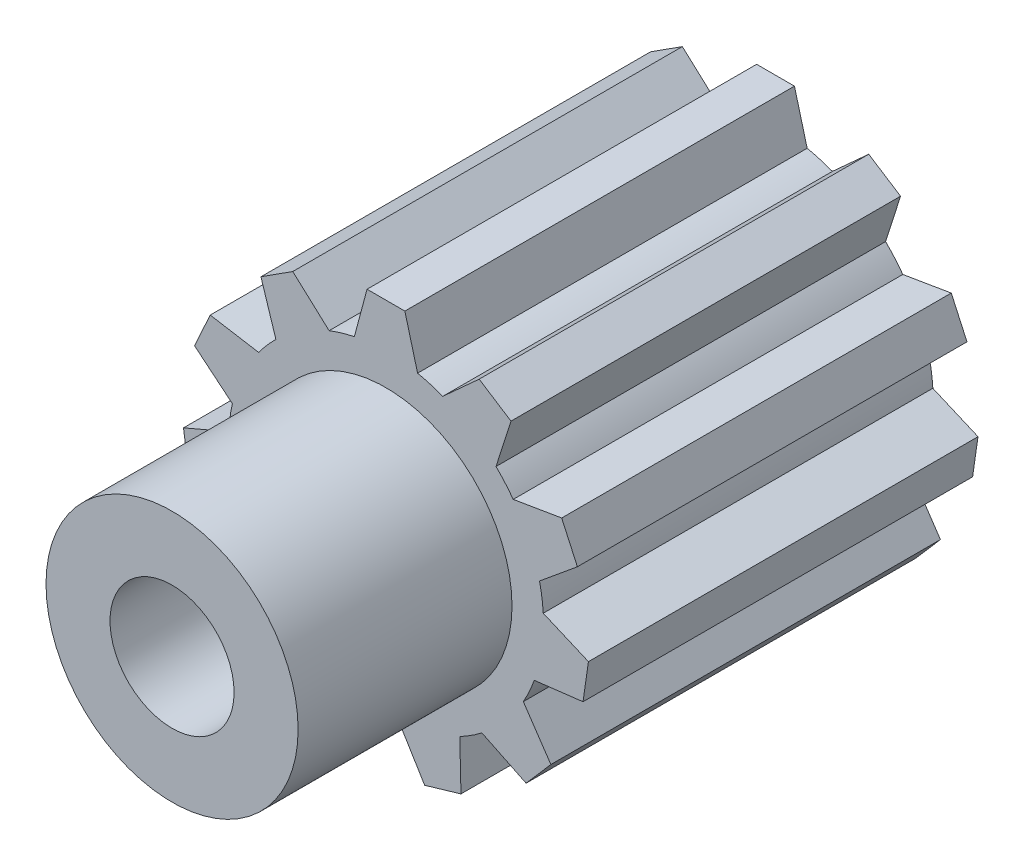
SolidWorks part; units mm, degrees
ref_plane "Front Plane" through (0, 0, 0) normal (0, 0, 1) x (1, 0, 0)
ref_plane "Top Plane" through (0, 0, 0) normal (0, 1, 0) x (1, 0, 0)
ref_plane "Right Plane" through (0, 0, 0) normal (1, 0, 0) x (0, 0, -1)
sketch "Sketch1" plane through (0, 0, 0) normal (0, 0, 1) x (1, 0, 0)
  circle A0 centre (0, 0) radius 6.35
  dimension "D1" = 12.7
extrude "Boss-Extrude1" add sketch "Sketch1" along normal blind 15.7
sketch "Sketch2" plane through (0, 0, 15.7) normal (0, 0, 1) x (1, 0, 0)
  line L0 (0, 0) -> (0, 8.1332) construction
  line L1 (0, 8.1332) -> (-0.762, 8.1332)
  line L2 (-0.762, 8.1332) -> (-1.3884, 5.7953)
  line L3 (0, 8.1332) -> (0.762, 8.1332)
  line L4 (0.762, 8.1332) -> (1.3884, 5.7953)
  line L5 (1.3884, 5.7953) -> (-1.3884, 5.7953)
  dimension "D1" = 75
  dimension "D2" = 75
  dimension "D3" = 0.762
  dimension "D4" = 0.762
  dimension "D5" = 5.7953
  dimension "D6" = 8.1332
extrude "Boss-Extrude2" add sketch "Sketch2" against normal blind 15.7
pattern_circular "CirPattern1" count 11 over 360 about axis through (0, 0, 0) along (0, 0, 1) of "Boss-Extrude2"
sketch "Sketch3" plane through (0, 0, 15.7) normal (0, 0, 1) x (1, 0, 0)
  circle A0 centre (0, 0) radius 5.08
  dimension "D1" = 10.16
extrude "Boss-Extrude3" add sketch "Sketch3" along normal blind 8.62 contours A0
sketch "Sketch4" plane through (0, 0, 24.32) normal (0, 0, 1) x (1, 0, 0)
  circle A0 centre (0, 0) radius 2.5
  dimension "D1" = 5
extrude "Cut-Extrude1" cut sketch "Sketch4" against normal through all
